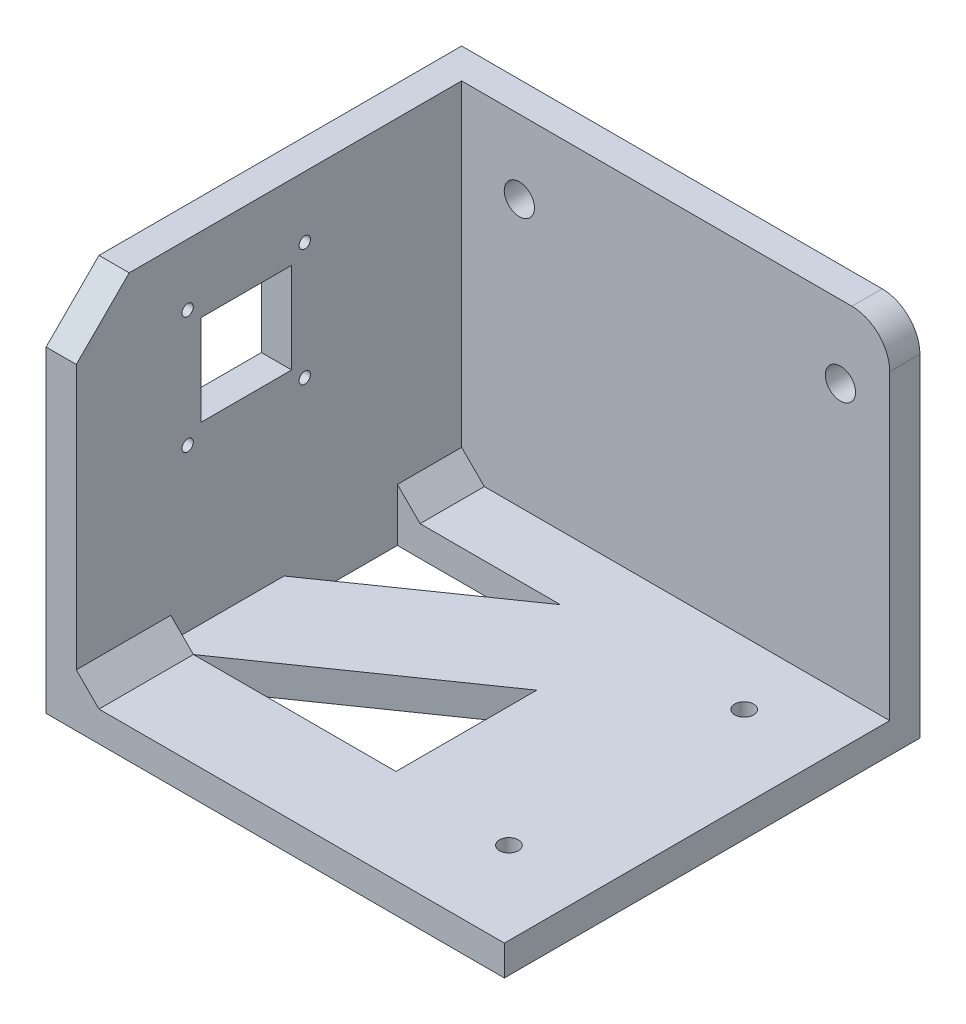
SolidWorks part; units mm, degrees
other "Markup1"
sketch "Sketch27" plane through (101.8454, 43.7034, -50.5416) normal (0.0088, 0.0285, -0.9996) x (-0.993, -0.1179, -0.0121)
ref_plane "Front Plane" through (0, 0, 0) normal (0, 0, 1) x (1, 0, 0)
ref_plane "Top Plane" through (0, 0, 0) normal (0, 1, 0) x (1, 0, 0)
ref_plane "Right Plane" through (0, 0, 0) normal (1, 0, 0) x (0, 0, -1)
sketch "Sketch2" plane through (0, 0, 0) normal (1, 0, 0) x (0, 0, -1)
  line L1 (22.5, 22.5) -> (-22.5, 22.5)
  line L2 (22.5, 22.5) -> (22.5, -22.5)
  line L3 (22.5, -22.5) -> (-22.5, -22.5)
  line L4 (-22.5, 22.5) -> (-22.5, -22.5)
  line L5 (22.5, 22.5) -> (-22.5, -22.5) construction
  line L6 (22.5, -22.5) -> (-22.5, 22.5) construction
  point P0 (0, 0)
  dimension "D1" = 45
  dimension "D2" = 45
extrude "Boss-Extrude1" add sketch "Sketch2" along normal blind 4 contours L3 L4 L1 L2
sketch "Sketch3" plane through (4, 0, 0) normal (1, 0, 0) x (0, 0, -1)
  line L0 (22.5, -22.5) -> (-22.5, -22.5) construction
  line L1 (7.7376, 14.365) -> (-7.7624, 14.365)
  line L2 (7.7376, 14.365) -> (7.7376, -1.135)
  line L3 (7.7376, -1.135) -> (-7.7624, -1.135)
  line L4 (-7.7624, 14.365) -> (-7.7624, -1.135)
  line L5 (7.7376, 14.365) -> (-7.7624, -1.135) construction
  line L6 (7.7376, -1.135) -> (-7.7624, 14.365) construction
  circle A0 centre (-7.7624, 14.365) radius 0.75
  circle A1 centre (-7.7624, -1.135) radius 0.75
  circle A2 centre (7.7376, -1.135) radius 0.75
  circle A3 centre (7.7376, 14.365) radius 0.75
  point P0 (-0.0124, 6.615)
  point P5 (-0.0124, 6.615)
  dimension "D3" = 1.5
  dimension "D4" = 1.5
  dimension "D5" = 1.5
  dimension "D6" = 1.5
  dimension "D1" = 15.5
  dimension "D2" = 15.5
  dimension "D7" = 29.115
  dimension "D8" = 0
extrude "Cut-Extrude1" cut sketch "Sketch3" against normal blind 5 contours A1 | A2 | A3 | A0
sketch "Sketch4" plane through (4, 0, 0) normal (1, 0, 0) x (0, 0, -1)
  line L0 (22.5, -22.5) -> (-22.5, -22.5) construction
  line L1 (6.0016, 12.615) -> (-5.9984, 12.615)
  line L2 (6.0016, 12.615) -> (6.0016, 0.615)
  line L3 (6.0016, 0.615) -> (-5.9984, 0.615)
  line L4 (-5.9984, 12.615) -> (-5.9984, 0.615)
  line L5 (6.0016, 12.615) -> (-5.9984, 0.615) construction
  line L6 (6.0016, 0.615) -> (-5.9984, 12.615) construction
  point P0 (0.0016, 6.615)
  point P9 (0.0016, 6.615)
  dimension "D1" = 12
  dimension "D2" = 12
  dimension "D3" = 29.115
  dimension "D4" = 0
  dimension "D5" = 0
extrude "Cut-Extrude2" cut sketch "Sketch4" against normal blind 5
sketch "Sketch5" plane through (0, 0, 0) normal (1, 0, 0) x (0, 0, -1)
  line L1 (-22.5, -22.5) -> (32.5, -22.5)
  line L2 (-22.5, -22.5) -> (-22.5, -26.5)
  line L3 (-22.5, -26.5) -> (32.5, -26.5)
  line L4 (32.5, -22.5) -> (32.5, -26.5)
  dimension "D1" = 55
  dimension "D2" = 4
extrude "Boss-Extrude2" add sketch "Sketch5" along normal blind 60.6541
sketch "Sketch7" plane through (0, 0, -22.5) normal (0, 0, -1) x (-1, 0, 0)
  line L0 (-60.6541, -26.5) -> (0, -26.5) construction
  line L1 (0, 22.5) -> (-4, 22.5)
  line L2 (0, 22.5) -> (0, -26.5)
  line L3 (0, -26.5) -> (-4, -26.5)
  line L4 (-4, 22.5) -> (-4, -26.5)
  dimension "D1" = 4
extrude "Boss-Extrude3" add sketch "Sketch7" along normal blind 10 contours L4 L3 L2 L1
sketch "Sketch9" plane through (4, 0, 0) normal (1, 0, 0) x (0, 0, -1)
  line L0 (-22.5, 15.5) -> (-22.5, 22.5)
  line L1 (-22.5, 22.5) -> (-15.5, 22.5)
  line L2 (-22.5, 15.5) -> (-15.5, 22.5)
extrude "Cut-Extrude6" cut sketch "Sketch9" against normal through all
sketch "Sketch11" plane through (0, 0, 22.5) normal (0, 0, 1) x (1, 0, 0)
  line L0 (4, -19.5) -> (7, -22.5)
  line L1 (4, 15.5) -> (4, -22.5) construction
  line L2 (60.6541, -22.5) -> (4, -22.5) construction
  line L3 (7, -22.5) -> (4, -22.5)
  line L4 (4, -22.5) -> (4, -19.5)
  dimension "D1" = 3
  dimension "D2" = 3
extrude "Boss-Extrude4" add sketch "Sketch11" against normal blind 55
sketch "Sketch12" plane through (0, -26.5, 0) normal (0, -1, 0) x (1, 0, 0)
  line L0 (0, 22.5) -> (0, -32.5) construction
  line L1 (4, -20) -> (33.8072, -20)
  line L2 (4, -20) -> (4, 10)
  line L3 (4, 10) -> (33.8072, 10)
  line L4 (33.8072, -20) -> (33.8072, 10)
  line L5 (60.6541, 22.5) -> (0, 22.5) construction
  dimension "D1" = 4
  dimension "D2" = 12.5
  dimension "D3" = 30
extrude "Cut-Extrude7" cut sketch "Sketch12" against normal through all
scale "Scale2" scale about centroid uniform scaling yes scale factor 2
sketch "Sketch21" plane through (0, -40.0167, 0) normal (0, -1, 0) x (-1, 0, 0)
  line L0 (10.6622, -25.2876) -> (4.6622, -25.2876)
  line L1 (4.6622, -25.2876) -> (-48.9521, 11.9916)
  line L2 (-48.9521, 34.7124) -> (-48.9521, -25.2876) construction
  line L3 (-48.9521, 11.9916) -> (-48.9521, 34.7124)
  line L4 (-48.9521, 34.7124) -> (-32.4833, 34.7124)
  line L5 (10.6622, 34.7124) -> (-48.9521, 34.7124) construction
  line L6 (-32.4833, 34.7124) -> (10.6622, 4.7124)
  line L7 (10.6622, -25.2876) -> (10.6622, 34.7124) construction
  line L8 (10.6622, 4.7124) -> (10.6622, -25.2876)
extrude "Boss-Extrude10" add sketch "Sketch21" against normal blind 8 contours L1 L3 L4 L6 L8 L0
sketch "Sketch29" plane through (0, -40.0167, 0) normal (0, -1, 0) x (1, 0, 0)
  line L0 (102.6461, 50.2876) -> (102.6461, -59.7124) construction
  line L1 (-18.6622, -59.7124) -> (102.6461, -59.7124)
  line L2 (-18.6622, -59.7124) -> (-18.6622, -51.7124)
  line L3 (-18.6622, -51.7124) -> (102.6461, -51.7124)
  line L4 (102.6461, -59.7124) -> (102.6461, -51.7124)
  dimension "D1" = 8
extrude "Boss-Extrude11" add sketch "Sketch29" against normal blind 98
sketch "Sketch30" plane through (0, -32.0167, 0) normal (0, 1, 0) x (1, 0, 0)
  circle A0 centre (80.8238, -27.2597) radius 2.5
  circle A1 centre (80.8238, 30) radius 2.5
extrude "Cut-Extrude8" cut sketch "Sketch30" against normal blind 98 contours A0
sketch "Sketch31" plane through (0, -32.0167, 0) normal (0, 1, 0) x (1, 0, 0)
  circle A0 centre (80.8238, 35.0169) radius 2.5
extrude "Cut-Extrude9" cut sketch "Sketch31" against normal blind 98
sketch "Sketch32" plane through (0, 0, -59.7124) normal (0, 0, -1) x (-1, 0, 0)
  line L0 (-102.6461, -40.0167) -> (18.6622, -40.0167) construction
  circle A0 centre (-89.6089, 38.7333) radius 4
  circle A1 centre (-4.6092, 38.4995) radius 4
  dimension "D1" = 85
  dimension "D2" = 78.75
extrude "Cut-Extrude10" cut sketch "Sketch32" against normal blind 98
fillet "Fillet1" radius 10 1 edges at (102.6461, 57.9833, -55.7124)
